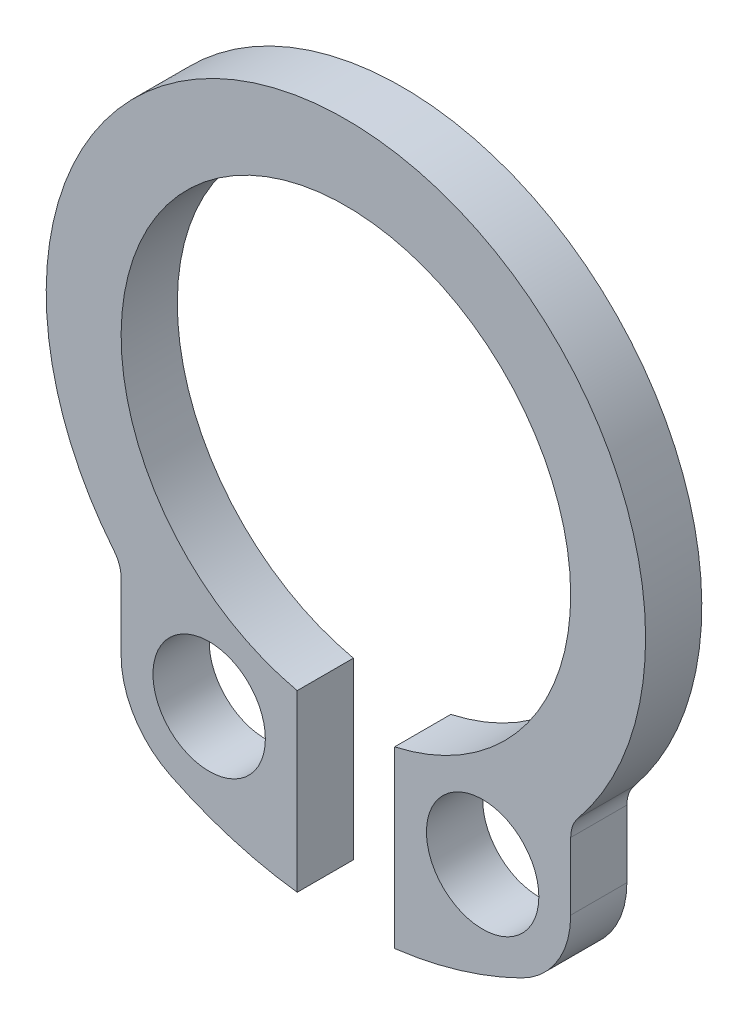
SolidWorks part; units mm, degrees
ref_plane "Face" through (0, 0, 0) normal (0, 0, 1) x (1, 0, 0)
ref_plane "Dessus" through (0, 0, 0) normal (0, 1, 0) x (1, 0, 0)
ref_plane "Droite" through (0, 0, 0) normal (1, 0, 0) x (0, 0, -1)
sketch "Esquisse1" plane through (0, 0, 0) normal (0, 0, 1) x (1, 0, 0)
  line L0 (-0.3978, -1.6033) -> (-0.3978, 0.728)
  line L1 (0.9022, -1.6033) -> (0.9022, 0.728)
  line L2 (-2.7478, -0.0426) -> (-2.7478, 0.8553)
  line L3 (3.2522, -0.0426) -> (3.2522, 0.8553)
  line L4 (0.2522, 3.6567) -> (0.2522, -1.8052) construction
  arc A0 (3.2522, 0.8553) -> (3.3482, 1.1243) centre (3.6772, 0.8553) cw
  circle A1 centre (-1.5728, -0.0426) radius 0.75
  arc A2 (-2.7478, -0.0426) -> (-2.0926, -1.0963) centre (-1.5728, -0.0426) ccw
  arc A3 (-2.0926, -1.0963) -> (-0.3978, -1.6033) centre (0.2522, 3.6567) ccw
  arc A4 (-2.7478, 0.8553) -> (-2.8438, 1.1243) centre (-3.1728, 0.8553) ccw
  arc A5 (2.5971, -1.0963) -> (3.2522, -0.0426) centre (2.0772, -0.0426) ccw
  arc A6 (3.3482, 1.1243) -> (-2.8438, 1.1243) centre (0.2522, 3.6567) ccw
  arc A7 (0.9022, -1.6033) -> (2.5971, -1.0963) centre (0.2522, 3.6567) ccw
  arc A8 (0.9022, 0.728) -> (-0.3978, 0.728) centre (0.2522, 3.6567) ccw
  circle A9 centre (2.0772, -0.0426) radius 0.75
extrude "Base-Extrusion" add sketch "Esquisse1" along normal blind 0.75
